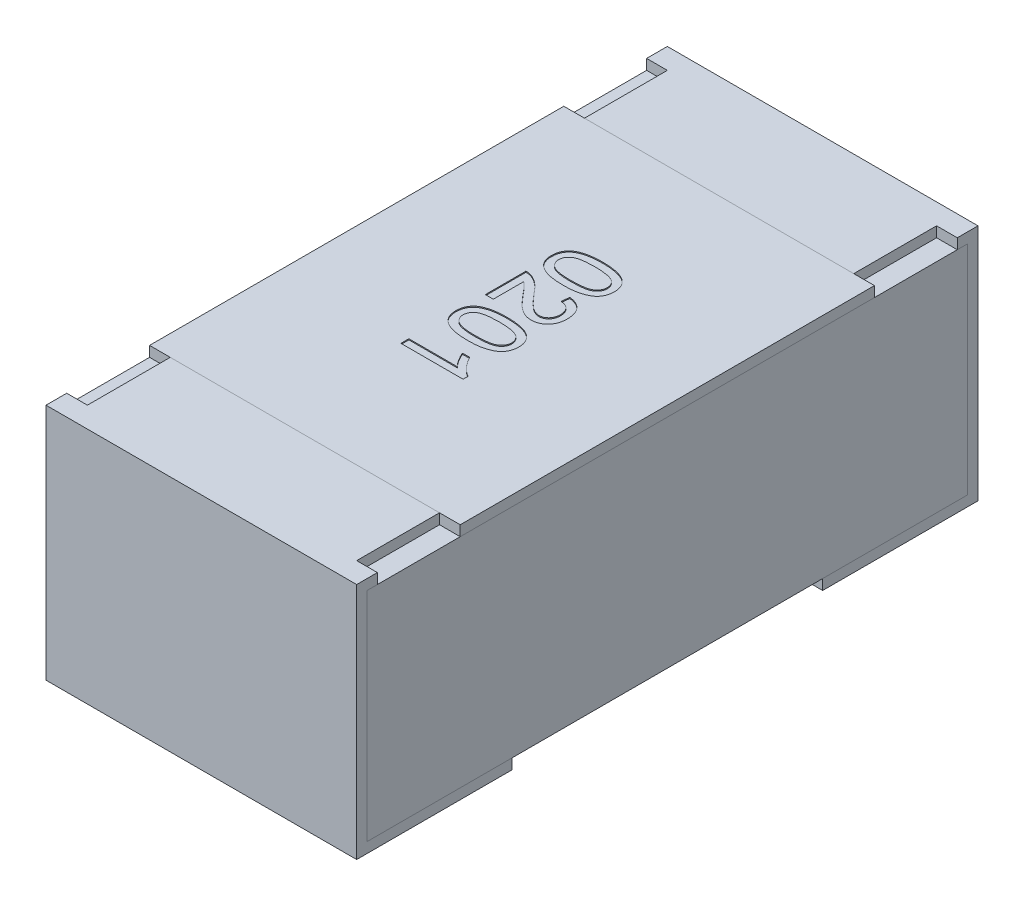
SolidWorks part; units mm, degrees
ref_plane "Front Plane" through (0, 0, 0) normal (0, 0, 1) x (1, 0, 0)
ref_plane "Top Plane" through (0, 0, 0) normal (0, 1, 0) x (1, 0, 0)
ref_plane "Right Plane" through (0, 0, 0) normal (1, 0, 0) x (0, 0, -1)
sketch "Sketch4" plane through (0, 0, 0) normal (1, 0, 0) x (0, 0, -1)
  line L0 (0, 0.1169) -> (0, -0.0721) construction
  line L1 (-0.3, 0) -> (0.3788, 0) construction
  line L2 (-0.3, 0.115) -> (-0.3, -0.115)
  line L3 (-0.3, -0.115) -> (-0.15, -0.115)
  line L4 (-0.2, 0.115) -> (-0.2, 0.105)
  line L5 (-0.2, 0.105) -> (-0.29, 0.105)
  line L6 (-0.29, 0.105) -> (-0.29, -0.105)
  line L7 (-0.29, -0.105) -> (-0.15, -0.105)
  line L8 (-0.15, -0.105) -> (-0.15, -0.115)
  line L9 (-0.2, 0.115) -> (-0.3, 0.115)
  line L10 (0.2, 0.115) -> (0.3, 0.115)
  line L11 (0.15, -0.105) -> (0.15, -0.115)
  line L12 (0.29, -0.105) -> (0.15, -0.105)
  line L13 (0.29, 0.105) -> (0.29, -0.105)
  line L14 (0.2, 0.105) -> (0.29, 0.105)
  line L15 (0.2, 0.115) -> (0.2, 0.105)
  line L16 (0.3, -0.115) -> (0.15, -0.115)
  line L17 (0.3, 0.115) -> (0.3, -0.115)
  dimension "LENGTH" = 0.3
  dimension "HEIGHT" = 0.23
  dimension "END CAP TOP LENGTH" = 0.1
  dimension "END CAP BOTTOM LENGTH" = 0.15
  dimension "D5" = 0.01
  dimension "D6" = 0.01
extrude "Boss-Extrude2" add sketch "Sketch4" along normal mid plane 0.3
sketch "Sketch5" plane through (0, 0, 0) normal (1, 0, 0) x (0, 0, -1)
  line L1 (-0.29, 0.105) -> (0.29, 0.105)
  line L2 (-0.29, 0.105) -> (-0.29, -0.105)
  line L3 (-0.29, -0.105) -> (0.29, -0.105)
  line L4 (0.29, 0.105) -> (0.29, -0.105)
extrude "Boss-Extrude3" add sketch "Sketch5" along normal up to surface and the other way up to surface separate body
sketch "Sketch6" plane through (0, 0.115, 0) normal (0, 1, 0) x (1, 0, 0)
  line L0 (-0.15, 0.3) -> (-0.15, 0.2) construction
  line L1 (-0.15, 0.28) -> (-0.13, 0.28)
  line L2 (-0.15, 0.28) -> (-0.15, 0.2)
  line L3 (-0.15, 0.2) -> (-0.13, 0.2)
  line L4 (-0.13, 0.28) -> (-0.13, 0.2)
  line L5 (0.15, 0.2) -> (-0.15, 0.2) construction
  line L6 (0, 0.0345) -> (0, -0.0345) construction
  line L7 (-0.0325, 0) -> (0.03, 0) construction
  line L8 (0.15, 0.28) -> (0.15, 0.2)
  line L9 (0.15, 0.2) -> (0.13, 0.2)
  line L10 (0.13, 0.28) -> (0.13, 0.2)
  line L11 (0.15, 0.28) -> (0.13, 0.28)
  line L12 (0.15, -0.28) -> (0.13, -0.28)
  line L13 (0.15, -0.28) -> (0.15, -0.2)
  line L14 (0.15, -0.2) -> (0.13, -0.2)
  line L15 (0.13, -0.28) -> (0.13, -0.2)
  line L16 (-0.15, -0.28) -> (-0.13, -0.28)
  line L17 (-0.15, -0.28) -> (-0.15, -0.2)
  line L18 (-0.15, -0.2) -> (-0.13, -0.2)
  line L19 (-0.13, -0.28) -> (-0.13, -0.2)
  dimension "TOP CUT WIDTH" = 0.02
  dimension "TOP CUT LENGTH" = 0.08
extrude "Cut-Extrude1" cut sketch "Sketch6" against normal up to surface (0.01 mm away) up to face at (0, 0.105, 0)
sketch "Sketch7" plane through (0, 0.105, 0) normal (0, 1, 0) x (1, 0, 0)
  line L1 (-0.15, 0.2) -> (0.15, 0.2)
  line L2 (-0.15, 0.2) -> (-0.15, -0.2)
  line L3 (-0.15, -0.2) -> (0.15, -0.2)
  line L4 (0.15, 0.2) -> (0.15, -0.2)
  line L5 (0.13, -0.2) -> (-0.13, -0.2) construction
  line L6 (0.13, 0.2) -> (-0.13, 0.2) construction
  line L7 (-0.15, -0.29) -> (-0.15, 0.29) construction
  line L8 (0.15, 0.29) -> (0.15, -0.29) construction
extrude "Boss-Extrude4" add sketch "Sketch7" along normal up to surface (0.01 mm away) separate body up to face at (0, 0.115, -0.265)
sketch "Sketch8" plane through (0, 0.115, 0) normal (0, 1, 0) x (1, 0, 0)
  line L0 (-0.0304, 0.1057) -> (-0.0304, -0.1057) construction
  line L1 (0, 0) -> (-0.0304, 0) construction
  text T0 "0201" font "Arial" height 0.06
extrude "TEXT0201" cut sketch "Sketch8" against normal blind 0.001
